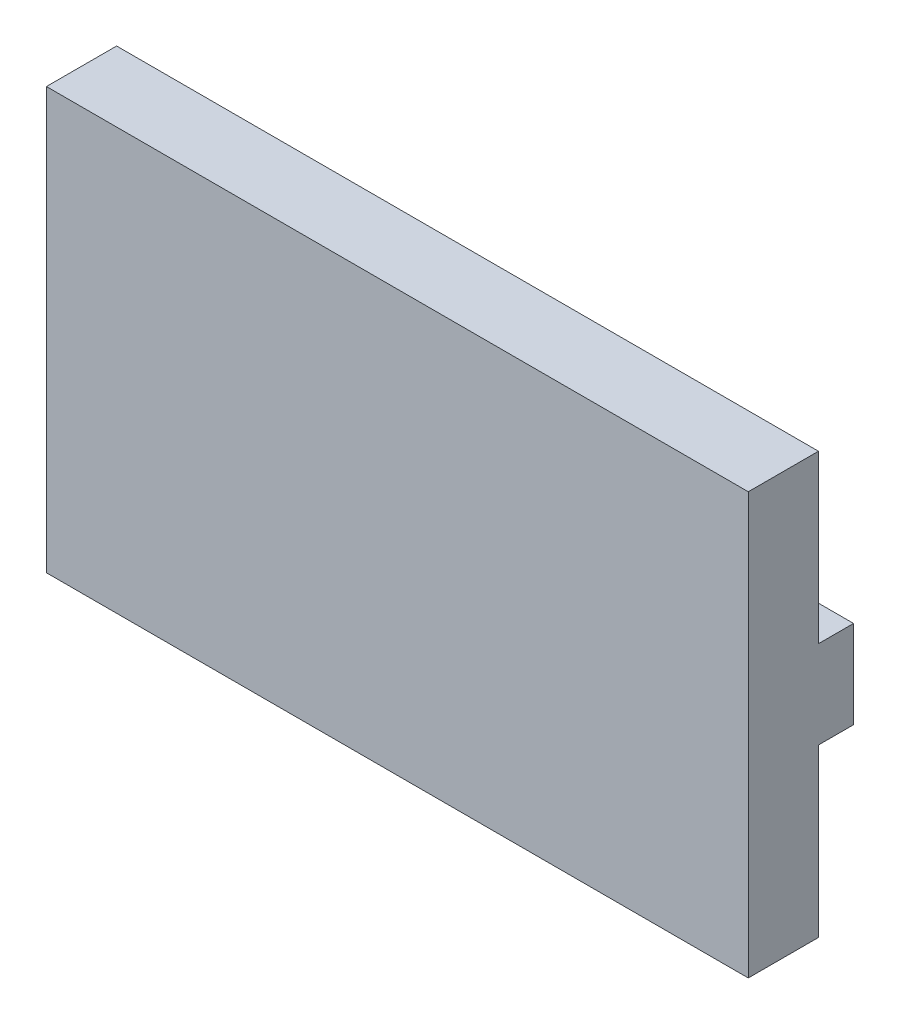
SolidWorks part; units mm, degrees
ref_plane "Plan de face" through (0, 0, 0) normal (0, 0, 1) x (1, 0, 0)
ref_plane "Plan de dessus" through (0, 0, 0) normal (0, 1, 0) x (1, 0, 0)
ref_plane "Plan de droite" through (0, 0, 0) normal (1, 0, 0) x (0, 0, -1)
sketch "Esquisse1" plane through (0, 0, 0) normal (0, 0, 1) x (1, 0, 0)
  line L1 (209.4675, 88.6738) -> (9.4675, 88.6738)
  line L2 (209.4675, 88.6738) -> (209.4675, -31.3262)
  line L3 (209.4675, -31.3262) -> (9.4675, -31.3262)
  line L4 (9.4675, 88.6738) -> (9.4675, -31.3262)
extrude "Boss.-Extru.1" add sketch "Esquisse1" along normal blind 20
ref_plane "Plan1" through (209.4675, -31.3262, 0) normal (0, 1, 0) x (1, 0, 0)
sketch "Esquisse2" plane through (0, 0, 0) normal (0, 0, -1) x (-1, 0, 0)
  line L0 (-209.4675, -31.3262) -> (-209.4675, 88.6738) construction
  line L1 (-209.4675, 41.1738) -> (-189.4675, 41.1738)
  line L2 (-209.4675, 41.1738) -> (-209.4675, 16.1738)
  line L3 (-209.4675, 16.1738) -> (-189.4675, 16.1738)
  line L4 (-189.4675, 41.1738) -> (-189.4675, 16.1738)
  line L6 (-176.4675, -31.3262) -> (-242.4675, -31.3262) construction
  dimension "D1" = 20
  dimension "D2" = 25
  dimension "D3" = 47.5
extrude "Boss.-Extru.2" add sketch "Esquisse2" along normal blind 10
